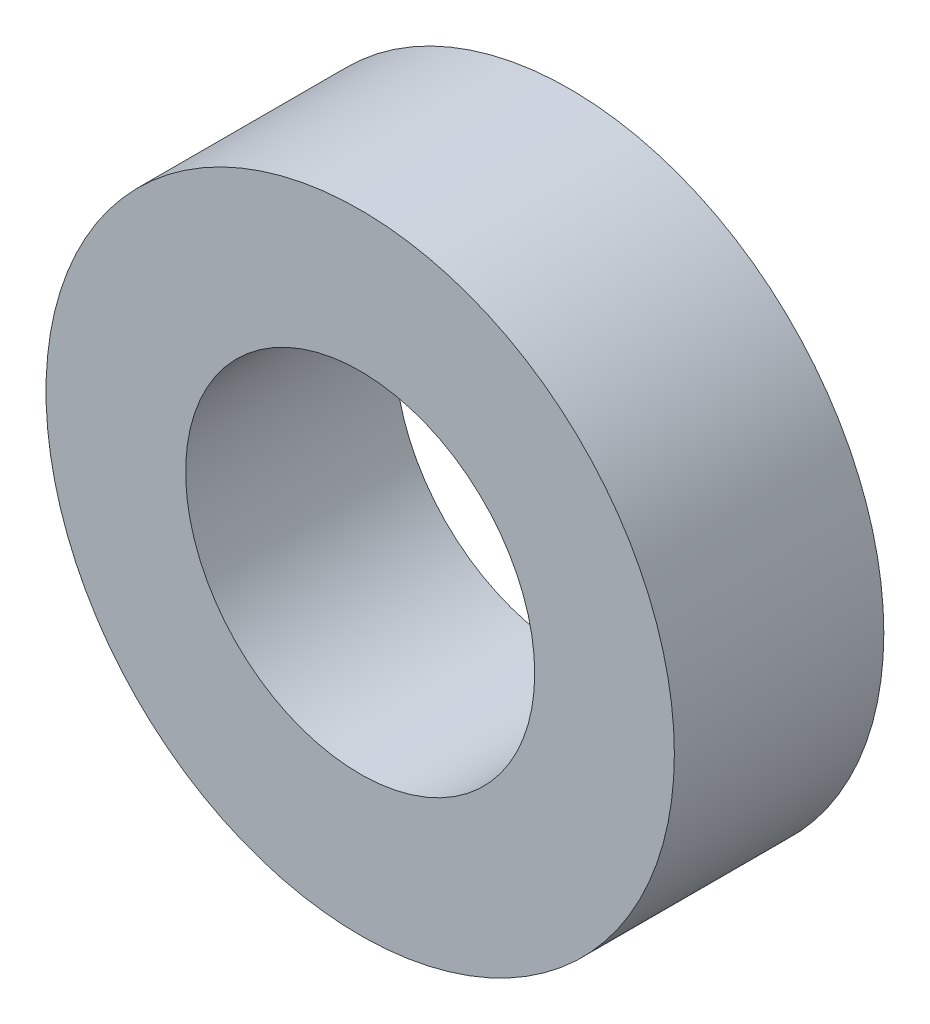
SolidWorks part; units mm, degrees
ref_plane "Front Plane" through (0, 0, 0) normal (0, 0, 1) x (1, 0, 0)
ref_plane "Top Plane" through (0, 0, 0) normal (0, 1, 0) x (1, 0, 0)
ref_plane "Right Plane" through (0, 0, 0) normal (1, 0, 0) x (0, 0, -1)
sketch "Sketch1" plane through (0, 0, 0) normal (0, 0, 1) x (1, 0, 0)
  circle A0 centre (0, 0) radius 4.5
  circle A1 centre (0, 0) radius 2.5
extrude "Boss-Extrude1" add sketch "Sketch1" along normal blind 3
